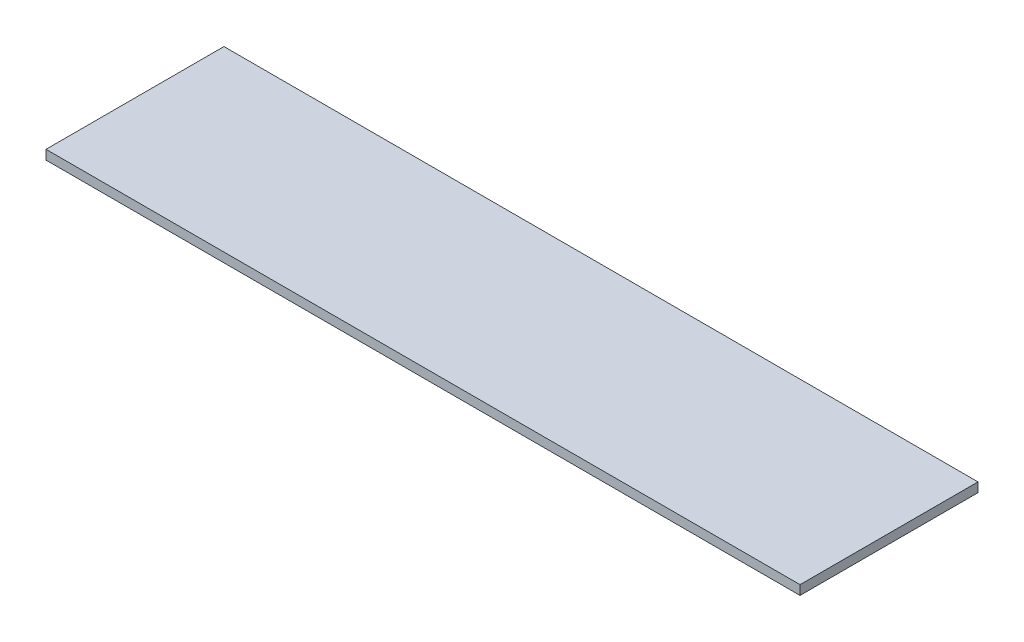
SolidWorks part; units mm, degrees
ref_plane "Front Plane" through (0, 0, 0) normal (0, 0, 1) x (1, 0, 0)
ref_plane "Top Plane" through (0, 0, 0) normal (0, 1, 0) x (1, 0, 0)
ref_plane "Right Plane" through (0, 0, 0) normal (1, 0, 0) x (0, 0, -1)
sketch "Sketch1" plane through (0, 0, 0) normal (0, 1, 0) x (1, 0, 0)
  line L1 (0, 0) -> (511.175, 0)
  line L2 (0, 0) -> (0, 120.65)
  line L3 (0, 120.65) -> (511.175, 120.65)
  line L4 (511.175, 0) -> (511.175, 120.65)
  dimension "D1" = 511.175
  dimension "D2" = 120.65
extrude "Boss-Extrude1" add sketch "Sketch1" along normal blind 6.35
